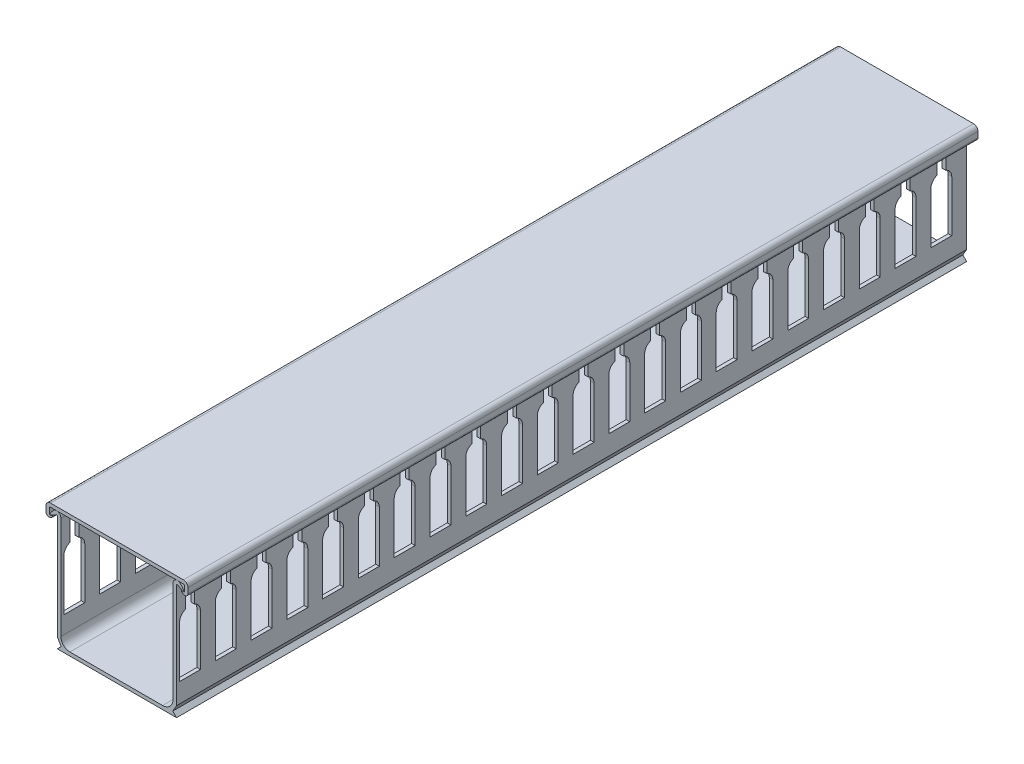
SolidWorks part; units mm, degrees
ref_plane "Front Plane" through (0, 0, 0) normal (0, 0, 1) x (1, 0, 0)
ref_plane "Top Plane" through (0, 0, 0) normal (0, 1, 0) x (1, 0, 0)
ref_plane "Right Plane" through (0, 0, 0) normal (1, 0, 0) x (0, 0, -1)
sketch "Sketch1" plane through (0, 0, 0) normal (0, 0, 1) x (1, 0, 0)
  line L0 (-20, 0) -> (20, 0)
  line L1 (-20, 3.5) -> (-20, 38.546)
  line L2 (-20, 0) -> (-18.7189, 1.2811)
  line L3 (-18.7189, 1.2811) -> (-20, 3.5)
  line L4 (-22.4196, 37.589) -> (-20.381, 38.766)
  line L5 (0, 0) -> (0, -17.0643) construction
  line L6 (22.4196, 37.589) -> (22.5, 37.889)
  line L7 (22.4196, 37.589) -> (20.381, 38.766)
  line L8 (20, 3.5) -> (20, 38.546)
  line L9 (18.7189, 1.2811) -> (20, 3.5)
  line L10 (-22.4196, 37.589) -> (-22.5, 37.889)
  line L11 (20, 0) -> (18.7189, 1.2811)
  line L12 (-18.8, 4.2) -> (-18.8, 38.546)
  line L13 (18.8, 3.5) -> (18.8, 38.546) construction
  line L14 (-17.2865, 1.2) -> (20, 1.2) construction
  line L15 (-15.8, 1.2) -> (15.3, 1.2)
  line L16 (18.8, 4.7) -> (18.8, 38.546)
  line L17 (-17.2865, 1.2) -> (-18.8, 3.8215) construction
  line L18 (-17.2865, 1.2) -> (-17.2865, 1.2) construction
  line L19 (-18.8, 3.8215) -> (-18.8, 38.546) construction
  arc A0 (-22.5, 37.889) -> (-21.2623, 39.5936) centre (-17.1014, 35.2708) cw
  arc A1 (22.5, 37.889) -> (21.2623, 39.5936) centre (17.1014, 35.2708) ccw
  arc A2 (20.381, 38.766) -> (20, 38.546) centre (20.254, 38.546) ccw
  arc A3 (-21.2623, 39.5936) -> (-18.8, 38.546) centre (-20.254, 38.546) cw
  arc A4 (21.2623, 39.5936) -> (18.8, 38.546) centre (20.254, 38.546) ccw
  arc A5 (-15.8, 1.2) -> (-18.8, 4.2) centre (-15.8, 4.2) cw
  arc A6 (-20.381, 38.766) -> (-20, 38.546) centre (-20.254, 38.546) cw
  arc A7 (15.3, 1.2) -> (18.8, 4.7) centre (15.3, 4.7) ccw
  arc A8 (-20.981, 39.8052) -> (-18.8, 38.546) centre (-20.254, 38.546) cw construction
  arc A9 (20.981, 39.8052) -> (18.8, 38.546) centre (20.254, 38.546) ccw construction
  dimension "D1" = 0.3
  dimension "D2" = 6
  dimension "D3" = 60
  dimension "D5" = 0.254
  dimension "D6" = 1.2
  dimension "D11" = 3
  dimension "D13" = 3.5
  dimension "D14" = 40
  dimension "D7" = 45
  dimension "D8" = 30
  dimension "D4" = 75
  dimension "D9" = 3.5
  dimension "D10" = 2.5
  dimension "D12" = 40
extrude "Boss-Extrude2" add sketch "Sketch1" along normal mid plane 1000 contours L0 L11 L9 L8 A2 L7 L6 A1 A4 L16 A7 L15 A5 L12 A3 A0 L10 L4 A6 L1 L3 L2
sketch "Sketch2" plane through (0, 0, 0) normal (1, 0, 0) x (0, 0, -1)
  line L0 (490, 30) -> (490, 40)
  line L1 (-500, 0) -> (500, 0) construction
  line L2 (500, 3.5) -> (500, 38.546) construction
  line L3 (488, 10) -> (495, 10)
  line L4 (495, 10) -> (495, 27.1716)
  line L6 (490, 40) -> (493, 40)
  line L7 (493, 30) -> (493, 40)
  line L8 (488, 10) -> (488, 27.1716)
  line L10 (500, 40) -> (-500, 40) construction
  arc A0 (495, 27.1716) -> (493, 30) centre (492, 27.1716) ccw
  arc A1 (488, 27.1716) -> (490, 30) centre (491, 27.1716) cw
  point P22 (491.5, 10)
  point P23 (491.5, 40)
  dimension "D1" = 3
  dimension "D2" = 10
  dimension "D3" = 10
  dimension "D4" = 7
  dimension "D5" = 5
  dimension "D6" = 3
extrude "Cut-Extrude1" cut sketch "Sketch2" against normal blind 82.296 and the other way blind 151.13
pattern_linear "LPattern1" count 83 spacing 12 along (0, 0, 1) of "Cut-Extrude1"
sketch "Sketch3" plane through (0, 0, -500) normal (0, 0, 1) x (1, 0, 0)
  line L0 (-22.6, 37.9) -> (-22.6, 39.7) construction
  line L1 (-22.6, 37.8781) -> (-22.6, 39.7)
  line L2 (22.3, 40) -> (-22.3, 40)
  line L4 (22.6, 37.8781) -> (22.6, 39.7)
  line L5 (22.6, 37.9) -> (22.6, 39.7) construction
  line L6 (22.3, 41.2) -> (-22.3, 41.2)
  line L7 (-22.3, 37.034) -> (-21.6, 37.4381)
  line L8 (-21.6, 37.4381) -> (-21.6, 38.0155)
  line L9 (-23.8, 37.9) -> (-23.8, 39.7)
  line L10 (-21.6, 38.0155) -> (-22.219, 37.6581)
  line L12 (22.3, 37.034) -> (21.6, 37.4381)
  line L14 (21.6, 38.0155) -> (22.219, 37.6581)
  line L15 (23.8, 37.9) -> (23.8, 39.7)
  line L16 (21.6, 37.4381) -> (21.6, 38.0155)
  arc A0 (-23.8, 37.9) -> (-22.3, 37.034) centre (-22.8, 37.9) ccw
  arc A1 (-22.6, 37.8781) -> (-22.219, 37.6581) centre (-22.346, 37.8781) ccw
  arc A2 (22.3, 37.034) -> (23.8, 37.9) centre (22.8, 37.9) ccw
  arc A3 (-22.3, 41.2) -> (-23.8, 39.7) centre (-22.3, 39.7) ccw
  arc A4 (-22.3, 40) -> (-22.6, 39.7) centre (-22.3, 39.7) ccw
  arc A5 (22.3, 41.2) -> (23.8, 39.7) centre (22.3, 39.7) cw
  arc A6 (22.3, 40) -> (22.6, 39.7) centre (22.3, 39.7) cw
  arc A7 (22.6, 37.8781) -> (22.219, 37.6581) centre (22.346, 37.8781) cw
  arc A9 (-18.8, 38.546) -> (-21.2623, 39.5936) centre (-20.254, 38.546) ccw construction
  point P35 (0, 40)
  dimension "D2" = 2.2
  dimension "D3" = 0.254
  dimension "D4" = 2.2
  dimension "D5" = 1.5
  dimension "D7" = 4.3
  dimension "D12" = 1
  dimension "D6" = 60
  dimension "D8" = 60
  dimension "D9" = 0.5
  dimension "D11" = 0.1
  dimension "D10" = 1.2
extrude "Boss-Extrude3" add sketch "Sketch3" along normal up to vertex separate body
sketch "Sketch4" plane through (0, 0, 500) normal (0, 0, 1) x (1, 0, 0)
  line L1 (-27.2695, 43.2212) -> (25.4448, 43.2212)
  line L2 (-27.2695, 43.2212) -> (-27.2695, -1.7887)
  line L3 (-27.2695, -1.7887) -> (25.4448, -1.7887)
  line L4 (25.4448, 43.2212) -> (25.4448, -1.7887)
extrude "Cut-Extrude2" cut sketch "Sketch4" against normal blind 735
